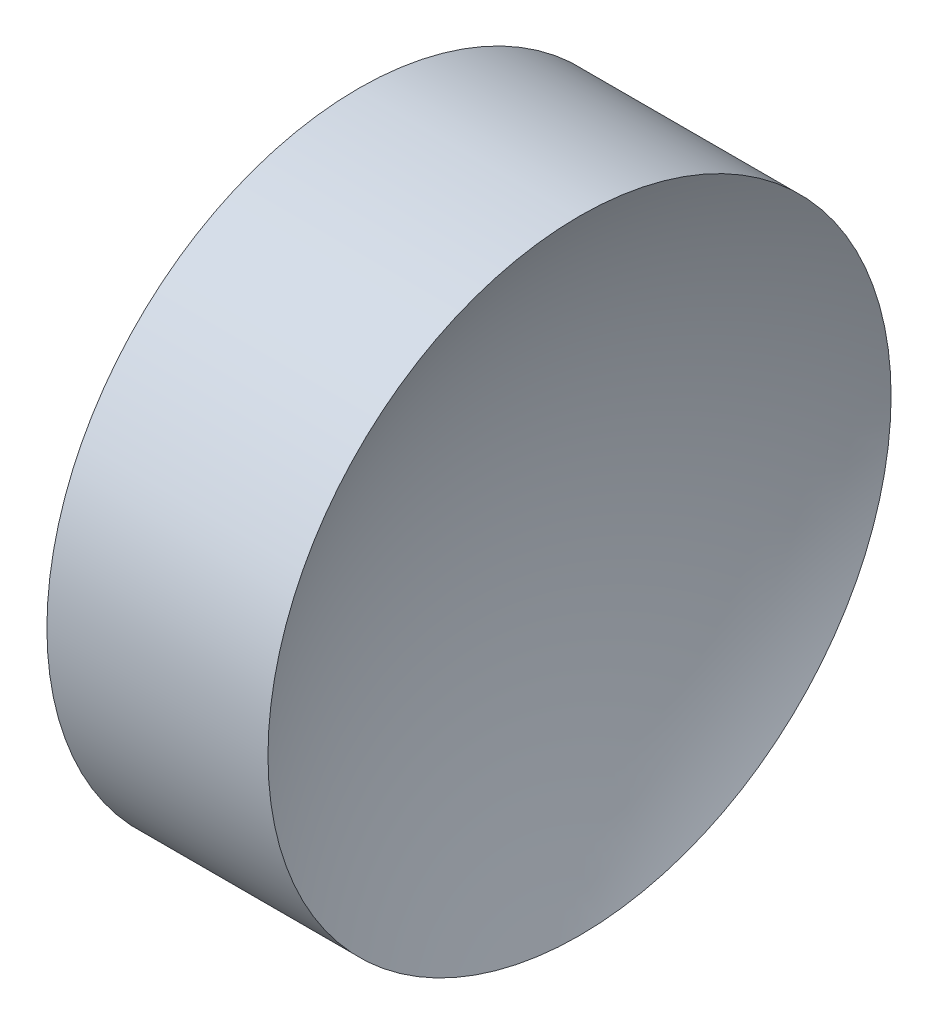
SolidWorks part; units mm, degrees
ref_plane "前视基准面" through (0, 0, 0) normal (0, 0, 1) x (1, 0, 0)
ref_plane "上视基准面" through (0, 0, 0) normal (0, 1, 0) x (1, 0, 0)
ref_plane "右视基准面" through (0, 0, 0) normal (1, 0, 0) x (0, 0, -1)
sketch "草图1" plane through (0, 0, 0) normal (0, 0, 1) x (1, 0, 0)
  line L0 (84.8997, 52.1781) -> (111.3291, 52.1781) construction
  line L1 (94.8404, 52.1781) -> (97.3404, 52.1781)
  line L3 (96.0904, 64.8781) -> (100.5959, 64.8781)
  line L4 (96.0904, 64.8781) -> (91.585, 64.8781)
  arc A0 (100.5959, 64.8781) -> (97.3404, 52.1781) centre (123.7404, 52.1781) ccw
  arc A1 (94.8404, 52.1781) -> (91.585, 64.8781) centre (68.4404, 52.1781) ccw
  dimension "D2" = 26.4
  dimension "D3" = 26.4
  dimension "D1" = 2.5
revolve "旋转1" add sketch "草图1" angle 360 about L0
